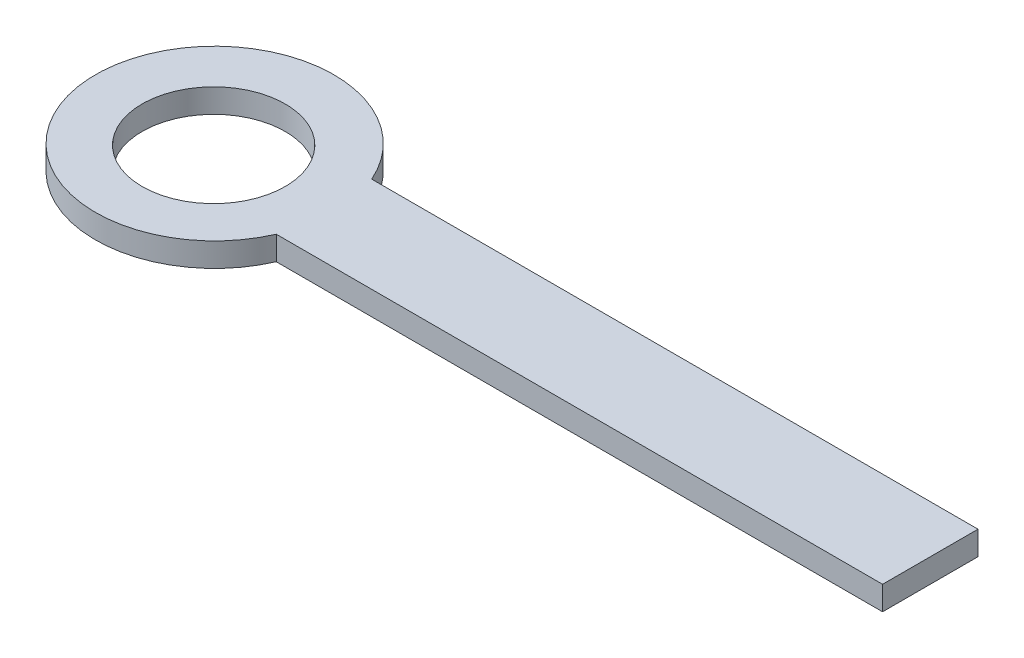
SolidWorks part; units mm, degrees
ref_plane "Front Plane" through (0, 0, 0) normal (0, 0, 1) x (1, 0, 0)
ref_plane "Top Plane" through (0, 0, 0) normal (0, 1, 0) x (1, 0, 0)
ref_plane "Right Plane" through (0, 0, 0) normal (1, 0, 0) x (0, 0, -1)
sketch "Sketch1" plane through (0, 0, 0) normal (0, 1, 0) x (1, 0, 0)
  line L1 (-53.4496, 12.6812) -> (200.7246, 12.6812)
  line L3 (-53.4496, -27.3188) -> (200.7246, -27.3188)
  line L4 (200.7246, 12.6812) -> (200.7246, -27.3188)
  arc A0 (-53.4496, 12.6812) -> (-53.4496, -27.3188) centre (-99.2754, -7.3188) ccw
extrude "Boss-Extrude1" add sketch "Sketch1" along normal blind 10 contours A0 L3 L4 L1
sketch "Sketch2" plane through (0, 10, 0) normal (0, 1, 0) x (1, 0, 0)
  circle A0 centre (-98.8741, -8.1318) radius 30
extrude "Cut-Extrude1" cut sketch "Sketch2" against normal through all contours A0
